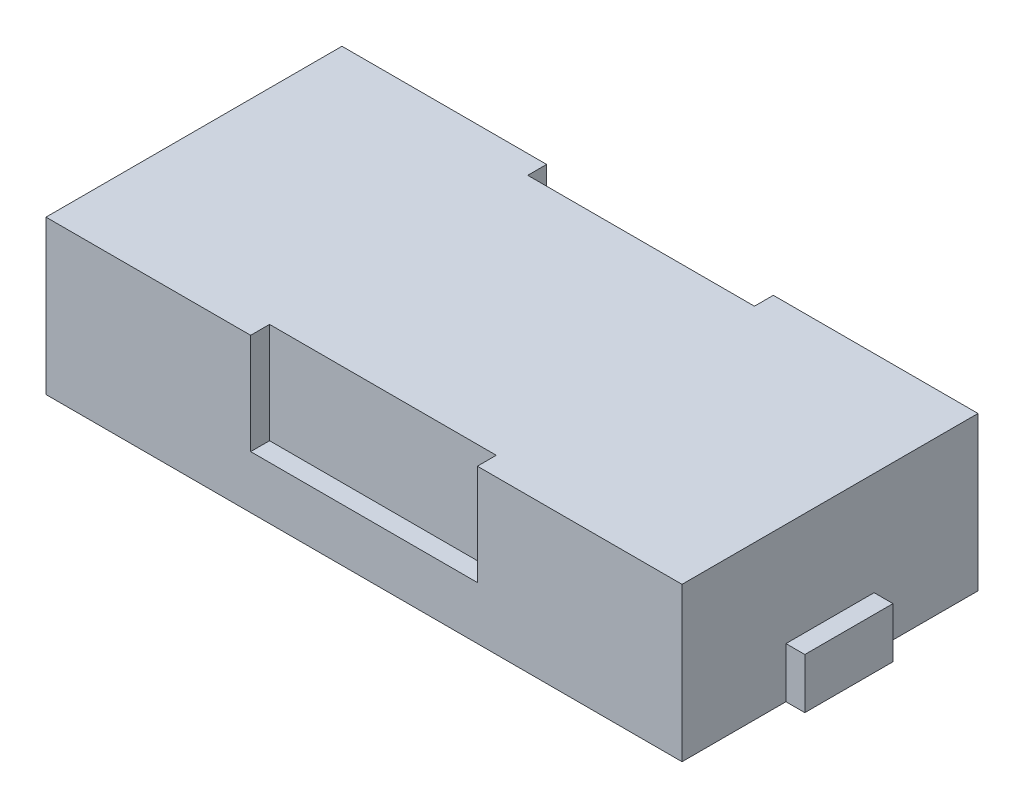
SolidWorks part; units mm, degrees
ref_plane "Спереди" through (0, 0, 0) normal (0, 0, 1) x (1, 0, 0)
ref_plane "Сверху" through (0, 0, 0) normal (0, 1, 0) x (1, 0, 0)
ref_plane "Справа" through (0, 0, 0) normal (1, 0, 0) x (0, 0, -1)
sketch "Эскиз1" plane through (0, 0, 0) normal (0, 1, 0) x (1, 0, 0)
  line L1 (-25.25, -11.75) -> (25.25, -11.75)
  line L2 (-25.25, -11.75) -> (-25.25, 11.75)
  line L3 (-25.25, 11.75) -> (25.25, 11.75)
  line L4 (25.25, -11.75) -> (25.25, 11.75)
  line L5 (-25.25, -11.75) -> (25.25, 11.75) construction
  line L6 (-25.25, 11.75) -> (25.25, -11.75) construction
  point P0 (0, 0)
  dimension "D1" = 23.5
  dimension "D2" = 50.5
extrude "Бобышка-Вытянуть1" add sketch "Эскиз1" along normal blind 12.2
sketch "Эскиз2" plane through (25.25, 0, 0) normal (1, 0, 0) x (0, 0, -1)
  line L0 (-11.75, 0) -> (11.75, 0) construction
  line L1 (-3.5, 0) -> (3.5, 0)
  line L2 (-3.5, 0) -> (-3.5, 4)
  line L3 (-3.5, 4) -> (3.5, 4)
  line L4 (3.5, 0) -> (3.5, 4)
  point P6 (0, 4)
  dimension "D1" = 4
  dimension "D2" = 7
extrude "Бобышка-Вытянуть2" add sketch "Эскиз2" along normal blind 1.5
sketch "Эскиз3" plane through (0, 0, 11.75) normal (0, 0, 1) x (1, 0, 0)
  line L0 (-25.25, 12.2) -> (25.25, 12.2) construction
  line L1 (-9, 12.2) -> (9, 12.2)
  line L2 (-9, 12.2) -> (-9, 4.2)
  line L3 (-9, 4.2) -> (9, 4.2)
  line L4 (9, 12.2) -> (9, 4.2)
  point P6 (0, 4.2)
  dimension "D1" = 18
  dimension "D2" = 8
extrude "Вырез-Вытянуть1" cut sketch "Эскиз3" against normal blind 1.5
mirror "Зеркальное отражение1" about plane through (0, 0, 0) normal (0, 0, 1) of "Вырез-Вытянуть1"
